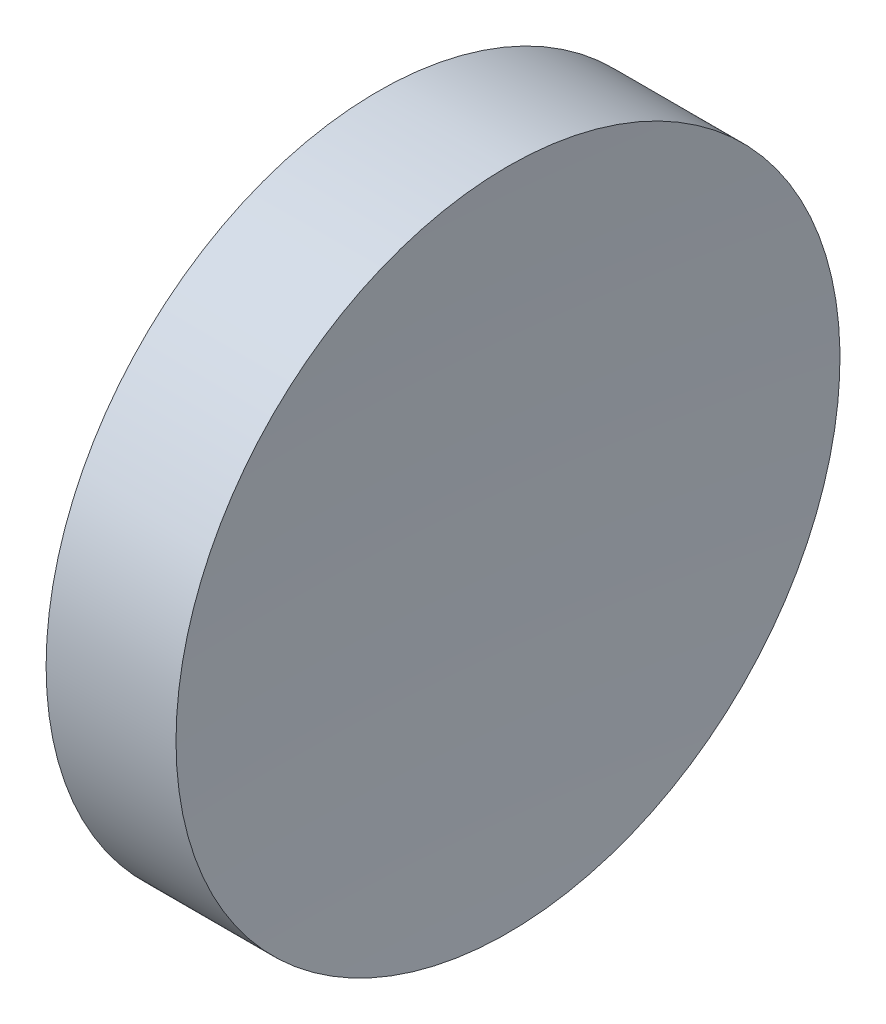
SolidWorks part; units mm, degrees
ref_plane "前视基准面" through (0, 0, 0) normal (0, 0, 1) x (1, 0, 0)
ref_plane "上视基准面" through (0, 0, 0) normal (0, 1, 0) x (1, 0, 0)
ref_plane "右视基准面" through (0, 0, 0) normal (1, 0, 0) x (0, 0, -1)
sketch "草图1" plane through (0, 0, 0) normal (0, 0, 1) x (1, 0, 0)
  line L0 (217.9703, 138.756) -> (265.5527, 138.756) construction
  line L1 (230.1853, 138.756) -> (230.1853, 163.756)
  line L2 (239.1853, 138.756) -> (230.1853, 138.756)
  line L3 (230.1853, 163.756) -> (239.9673, 163.756)
  arc A0 (239.9673, 163.756) -> (239.1853, 138.756) centre (639.1853, 138.756) ccw
  dimension "D1" = 400
  dimension "D2" = 9.782
revolve "旋转1" add sketch "草图1" angle 360 about L0
